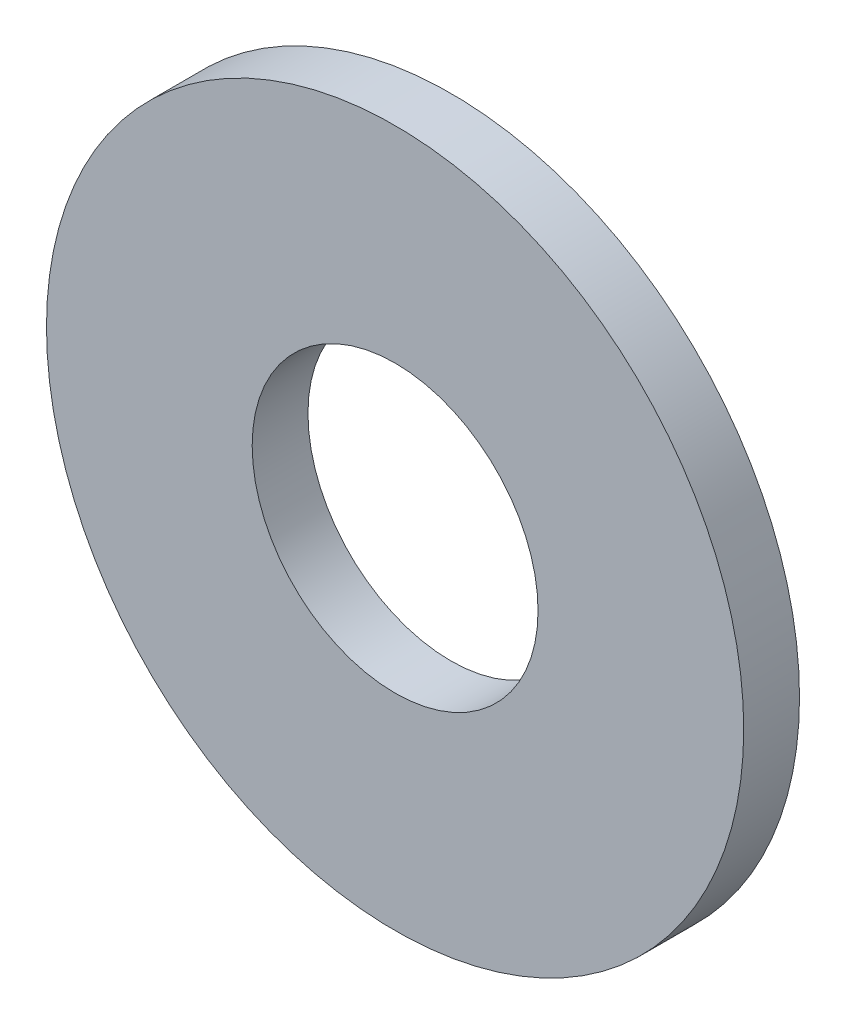
SolidWorks part; units mm, degrees
ref_plane "Front Plane" through (0, 0, 0) normal (0, 0, 1) x (1, 0, 0)
ref_plane "Top Plane" through (0, 0, 0) normal (0, 1, 0) x (1, 0, 0)
ref_plane "Right Plane" through (0, 0, 0) normal (1, 0, 0) x (0, 0, -1)
sketch "Sketch1" plane through (0, 0, 0) normal (0, 0, 1) x (1, 0, 0)
  circle A0 centre (0, 0) radius 2.05
  circle A1 centre (0, 0) radius 5
  dimension "D1" = 4.1
  dimension "D2" = 10
extrude "Boss-Extrude1" add sketch "Sketch1" along normal blind 0.8
